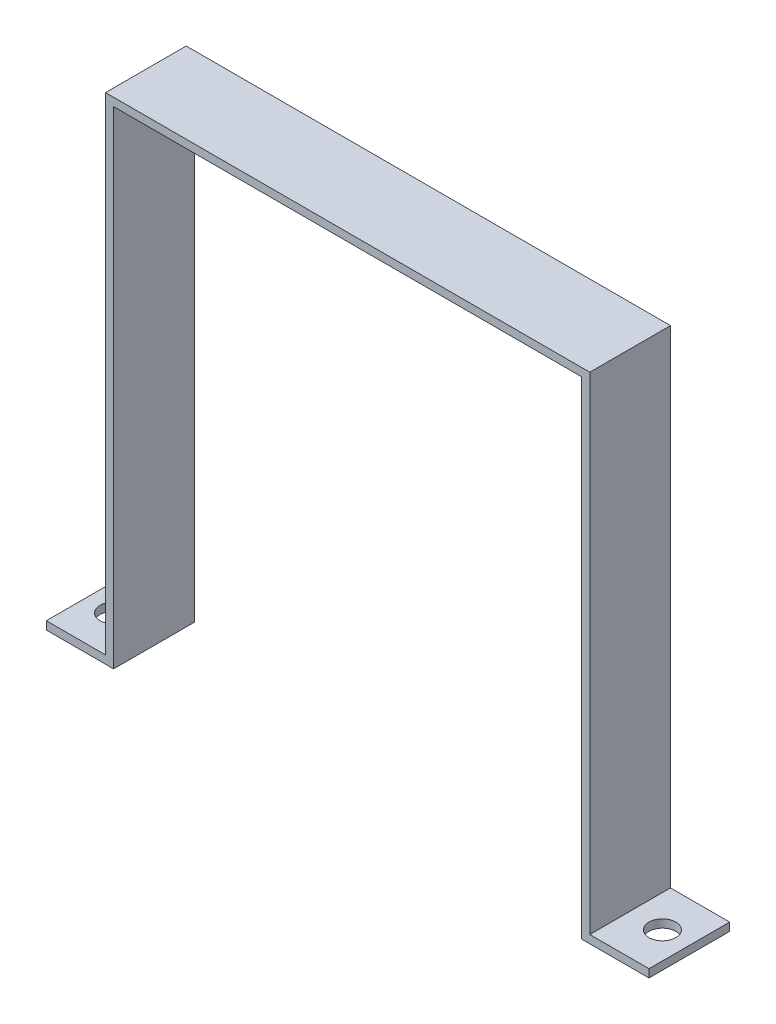
SolidWorks part; units mm, degrees
ref_plane "Front Plane" through (0, 0, 0) normal (0, 0, 1) x (1, 0, 0)
ref_plane "Top Plane" through (0, 0, 0) normal (0, 1, 0) x (1, 0, 0)
ref_plane "Right Plane" through (0, 0, 0) normal (1, 0, 0) x (0, 0, -1)
sketch "Sketch1" plane through (0, 0, 0) normal (0, 0, 1) x (1, 0, 0)
  line L0 (-87, 0) -> (87, 0) construction
  line L1 (-87, 0) -> (-87, 181)
  line L2 (-87, 181) -> (87, 181)
  line L3 (87, 181) -> (87, 0)
  line L4 (87, 0) -> (112, 0)
  line L5 (112, 0) -> (112, 3)
  line L6 (112, 3) -> (90, 3)
  line L7 (90, 3) -> (90, 184)
  line L8 (90, 184) -> (-90, 184)
  line L9 (-90, 184) -> (-90, 3)
  line L10 (-90, 3) -> (-112, 3)
  line L11 (-112, 3) -> (-112, 0)
  line L12 (-112, 0) -> (-87, 0)
  dimension "D1" = 3
  dimension "D2" = 3
  dimension "D3" = 3
  dimension "D4" = 3
  dimension "D5" = 181
  dimension "D6" = 174
  dimension "D7" = 87
  dimension "D8" = 25
  dimension "D9" = 25
  dimension "D10" = 3
extrude "Boss-Extrude1" add sketch "Sketch1" along normal blind 30
sketch "Sketch2" plane through (0, 3, 0) normal (0, 1, 0) x (1, 0, 0)
  line L0 (-90, 0) -> (-112, 0) construction
  line L2 (-90, -30) -> (-90, 0) construction
  line L3 (90, -30) -> (90, 0) construction
  line L4 (112, 0) -> (90, 0) construction
  circle A0 centre (-102, -15) radius 5
  circle A1 centre (102, -15) radius 5
  dimension "D2" = 10
  dimension "D6" = 10
  dimension "D1" = 15
  dimension "D3" = 12
  dimension "D4" = 12
  dimension "D5" = 15
extrude "Cut-Extrude1" cut sketch "Sketch2" against normal blind 30
